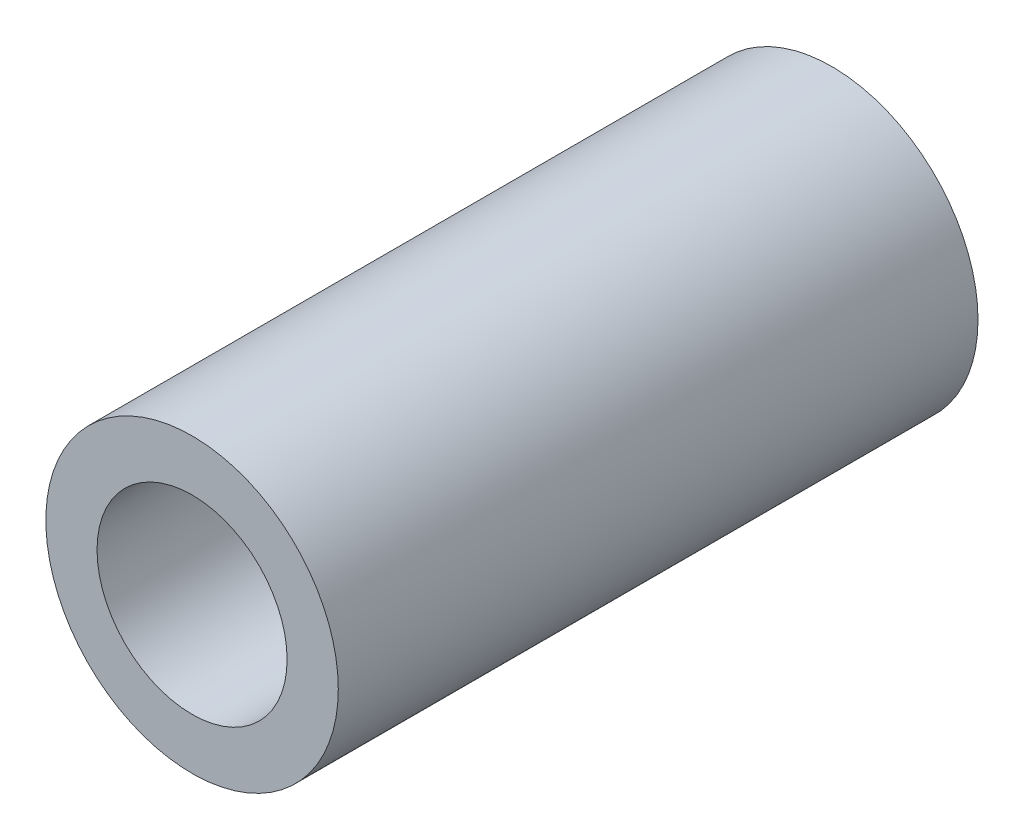
SolidWorks part; units mm, degrees
ref_plane "Płaszczyzna przednia" through (0, 0, 0) normal (0, 0, 1) x (1, 0, 0)
ref_plane "Płaszczyzna górna" through (0, 0, 0) normal (0, 1, 0) x (1, 0, 0)
ref_plane "Płaszczyzna prawa" through (0, 0, 0) normal (1, 0, 0) x (0, 0, -1)
sketch "Szkic1" plane through (0, 0, 0) normal (0, 0, 1) x (1, 0, 0)
  circle A0 centre (0, 0) radius 5.2
  circle A1 centre (0, 0) radius 8
  dimension "D1" = 10.4
  dimension "D2" = 16
extrude "Dodanie-wyciągnięcie1" add sketch "Szkic1" along normal blind 35
